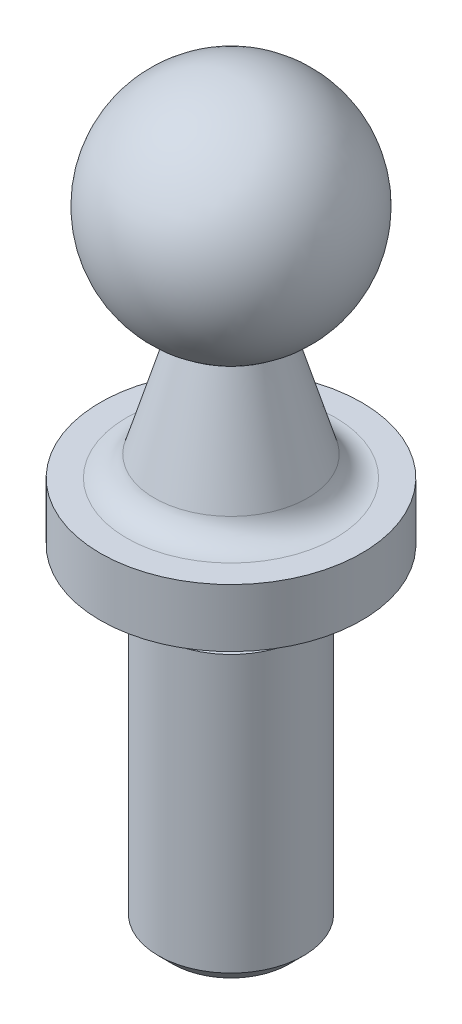
SolidWorks part; units mm, degrees
ref_plane "Plan1" through (0, 0, 0) normal (0, 0, 1) x (1, 0, 0)
ref_plane "Plan2" through (0, 0, 0) normal (0, 1, 0) x (1, 0, 0)
ref_plane "Plan3" through (0, 0, 0) normal (1, 0, 0) x (0, 0, -1)
sketch "Esquisse2" plane through (0, 0, 0) normal (0, 0, 1) x (1, 0, 0)
  line L0 (0, 10.1876) -> (0, -28.9715) construction
  line L1 (1.5, -7.5) -> (2.85, -12)
  line L2 (2.85, -12) -> (4.5, -12)
  line L3 (4.5, -12) -> (4.5, -14)
  line L4 (4.5, -14) -> (2.5, -14)
  line L5 (2.5, -15.5) -> (2.5, -25.5)
  line L6 (2.5, -25.5) -> (0, -25.5)
  line L7 (0, 0) -> (0, -25.5)
  line L8 (2.5, -14) -> (2.0024, -14)
  line L9 (2.0024, -14) -> (2.0024, -15.5)
  line L10 (2.0024, -15.5) -> (2.5, -15.5)
  arc A0 (0, 0) -> (1.5, -7.5) centre (0, -3.9) cw
  dimension "D1" = 3.9
  dimension "D2" = 7.5
  dimension "D3" = 4.5
  dimension "D4" = 2.85
  dimension "D5" = 4.5
  dimension "D6" = 2
  dimension "D7" = 5
  dimension "D8" = 11.5
  dimension "D9" = 2.0024
  dimension "D10" = 1.5
revolve "Base-Révolution" add sketch "Esquisse2"
cosmetic thread "Représentation de filetage1"
chamfer "Chanfrein1" distance 0.5 angle 45
fillet "Congé1" radius 1
